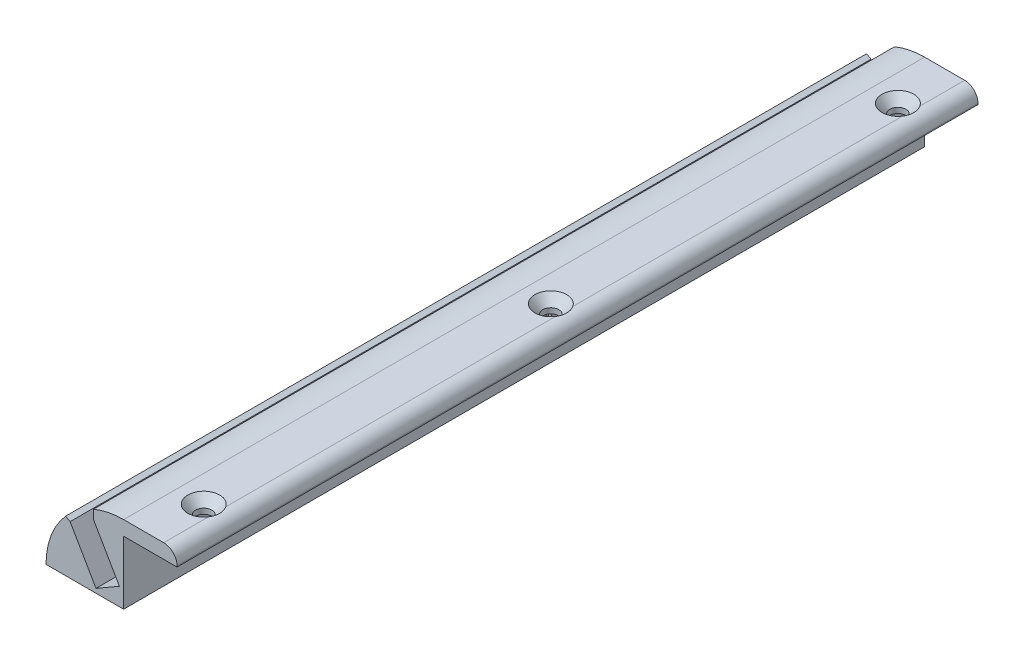
SolidWorks part; units mm, degrees
ref_plane "Front Plane" through (0, 0, 0) normal (0, 0, 1) x (1, 0, 0)
ref_plane "Top Plane" through (0, 0, 0) normal (0, 1, 0) x (1, 0, 0)
ref_plane "Right Plane" through (0, 0, 0) normal (1, 0, 0) x (0, 0, -1)
sketch "Sketch1" plane through (0, 0, 0) normal (0, 0, 1) x (1, 0, 0)
  line L0 (-43.8658, 7.3279) -> (-25.4, 7.3279)
  line L1 (-127, 7.3279) -> (127, 7.3279) construction
  line L2 (-25.4, 7.3279) -> (-25.4, 21.9837)
  line L3 (-25.4, 22.3647) -> (-14.6818, 22.3647)
  line L4 (-25.4, 21.9837) -> (228.6, 21.9837) construction
  line L5 (-25.4, 22.3647) -> (-25.4, 21.9837)
  line L6 (-38.1345, 19.0062) -> (-41.9445, 21.2059)
  line L7 (-41.9445, 21.2059) -> (-32.5693, 26.6187)
  line L8 (-32.5693, 26.6187) -> (-32.5693, 22.2193)
  line L9 (-25.4, 7.3279) -> (-34.6329, 23.3198) construction
  line L14 (-25.4, 25.7937) -> (-15.875, 25.7937)
  line L15 (-12.7, 22.6187) -> (-12.7, 22.3647)
  line L16 (-12.7, 22.3647) -> (-14.6818, 22.3647)
  line L18 (-38.1345, 19.0062) -> (-31.975, 8.3377)
  line L19 (-31.975, 8.3377) -> (-26.4098, 11.5508)
  line L20 (-26.4098, 11.5508) -> (-32.5693, 22.2193)
  line L21 (-32.5693, 22.2193) -> (-38.1345, 19.0062)
  line L22 (-38.1345, 19.0062) -> (-31.975, 8.3377)
  line L23 (-31.975, 8.3377) -> (-26.4098, 11.5508)
  line L24 (-26.4098, 11.5508) -> (-32.5693, 22.2193)
  line L25 (-32.5693, 22.2193) -> (-38.1345, 19.0062)
  circle A0 centre (-25.4, 7.3279) radius 18.4658
  arc A1 (-15.875, 25.7937) -> (-12.7, 22.6187) centre (-15.875, 22.6187) cw
  point P3 (-25.4, 25.7937)
  point P7 (-25.4, 21.9837)
  point P14 (0, 0)
  point P20 (-27.0497, 10.1852)
  point P24 (-12.455, 22.3647)
  dimension "D8" = 3.175
  dimension "D1" = 3.81
  dimension "D2" = 0.381
  dimension "D3" = 60
  dimension "D4" = 0.1905
  dimension "D5" = 30
  dimension "D6" = 30
  dimension "D7" = 3.81
  dimension "D9" = 12.7
extrude "Boss-Extrude1" add sketch "Sketch1" along normal mid plane 190.5 contours L0 L9 L23 L22 L6 A0 | L9 L2 L5 L3 A0 L8 L24 L23 | A1 L14 A0 L16 L15
ref_plane "Plane1" through (0, 0, 82.55) normal (0, 0, 1) x (1, 0, 0)
sketch "Sketch4" plane through (0, 0, 82.55) normal (0, 0, 1) x (1, 0, 0)
  line L0 (-17.145, 22.3647) -> (-17.145, 23.6347)
  line L1 (-25.4, 22.3647) -> (-12.7, 22.3647) construction
  line L2 (-17.145, 23.6347) -> (-13.833, 27.4447)
  line L3 (-13.833, 27.4447) -> (-19.05, 27.4447)
  line L4 (-19.05, 27.4447) -> (-19.05, 22.3647)
  line L5 (-19.05, 22.3647) -> (-17.145, 22.3647)
  point P7 (-19.799, 22.3647)
  dimension "D1" = 1.905
  dimension "D2" = 1.27
  dimension "D3" = 41
  dimension "D4" = 5.08
  dimension "D5" = 6.35
revolve "Cut-Revolve1" cut sketch "Sketch4" angle 360 about L4
pattern_linear "LPattern1" count 3 spacing 82.55 along (0, 0, -1) of "Cut-Revolve1"
sketch "Sketch5" plane through (-25.4, 0, 0) normal (1, 0, 0) x (0, 0, -1)
  line L0 (-69.1647, 14.9479) -> (67.826, 14.9479) construction
  line L1 (-95.25, 7.3279) -> (95.25, 7.3279) construction
  text T0 "<b>Headboard Ceiling LED Mount V1</b>" font "Century Gothic" height 5.08
  point P3 (0, 14.9479)
  point P4 (-4.4241, 11.5921)
  point P6 (0, 11.4996)
  dimension "D1" = 7.62
extrude "Cut-Extrude2" cut sketch "Sketch5" against normal blind 0.635
